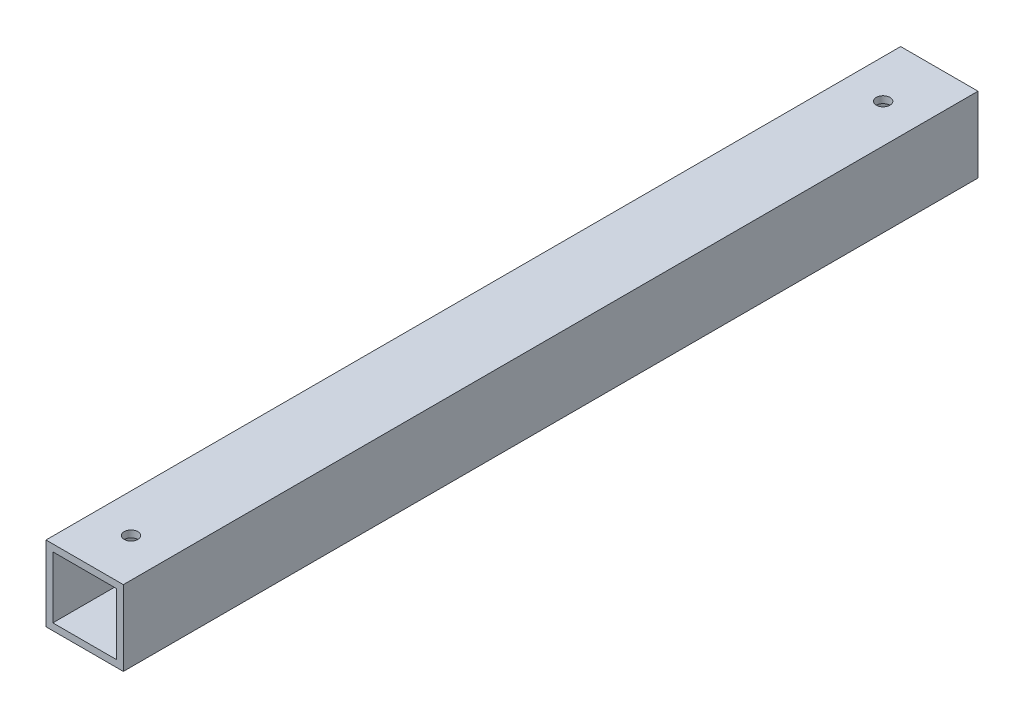
SolidWorks part; units mm, degrees
ref_plane "Front Plane" through (0, 0, 0) normal (0, 0, 1) x (1, 0, 0)
ref_plane "Top Plane" through (0, 0, 0) normal (0, 1, 0) x (1, 0, 0)
ref_plane "Right Plane" through (0, 0, 0) normal (1, 0, 0) x (0, 0, -1)
sketch "Sketch1" plane through (0, 0, 0) normal (0, 0, 1) x (1, 0, 0)
  line L1 (-20.625, 20) -> (20.625, 20)
  line L2 (-20.625, 20) -> (-20.625, -20)
  line L3 (-20.625, -20) -> (20.625, -20)
  line L4 (20.625, 20) -> (20.625, -20)
  line L5 (-20.625, 20) -> (20.625, -20) construction
  line L6 (-20.625, -20) -> (20.625, 20) construction
  point P0 (0, 0)
  dimension "D1" = 40
extrude "Extrude-Thin1" add sketch "Sketch1" along normal mid plane 500 thin thin type mid plane wall 4
sketch "Sketch2" plane through (0, 22, 0) normal (0, 1, 0) x (1, 0, 0)
  circle A0 centre (0, 217.1317) radius 4
  circle A1 centre (0, -222.8683) radius 4
  dimension "D1" = 440
extrude "Cut-Extrude1" cut sketch "Sketch2" against normal through all
